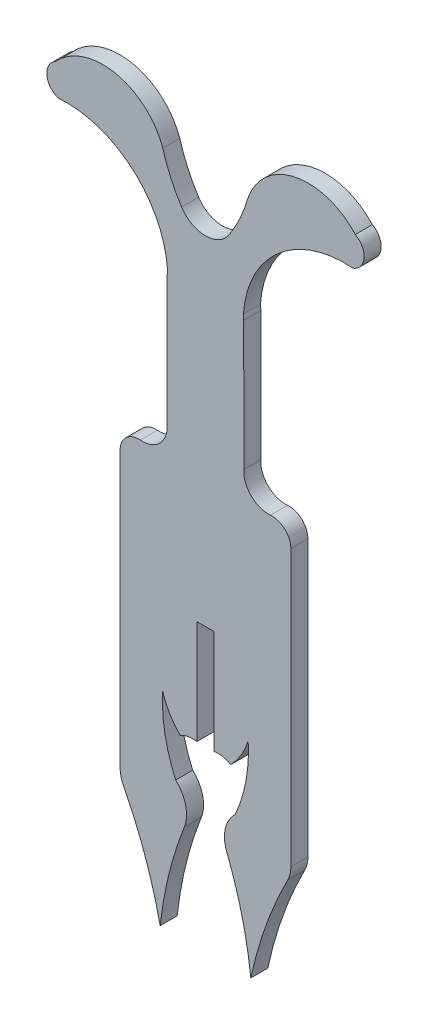
SolidWorks part; units mm, degrees
ref_plane "Front Plane" through (0, 0, 0) normal (0, 0, 1) x (1, 0, 0)
ref_plane "Top Plane" through (0, 0, 0) normal (0, 1, 0) x (1, 0, 0)
ref_plane "Right Plane" through (0, 0, 0) normal (1, 0, 0) x (0, 0, -1)
sketch "Sketch1" plane through (0, 0, 0) normal (0, 0, 1) x (1, 0, 0)
  line L0 (0.7584, -14.5146) -> (0.7564, -5.2296)
  line L1 (0.7564, -5.2296) -> (-0.7676, -5.2286)
  line L2 (-0.7676, -5.2286) -> (-0.7676, -14.5136)
  line L3 (-7.6306, -20.0152) -> (-7.6319, 4.6269)
  line L4 (-3.4282, 8.6563) -> (-3.4315, 20.1838)
  line L5 (3.42, 20.1837) -> (3.4215, 8.6564)
  line L6 (7.6282, 4.629) -> (7.6318, -20.0085)
  line L7 (-0.001, -5.2309) -> (-0.001, 45.1818) construction
  arc A0 (-0.7676, -14.5136) -> (-2.2638, -14.7873) centre (-1.1294, -16.7622) ccw
  arc A1 (-1.9033, -21.7277) -> (-2.6639, -18.445) centre (-4.6657, -20.6383) ccw
  arc A2 (-5.8206, 6.2988) -> (-7.6319, 4.6269) centre (-5.9547, 4.627) ccw
  arc A3 (-5.8206, 6.2988) -> (-3.4282, 8.6563) centre (-5.643, 8.5113) ccw
  arc A4 (3.42, 20.1837) -> (3.3881, 20.6504) centre (-0.0057, 20.1837) ccw
  arc A5 (3.4215, 8.6564) -> (5.8136, 6.3009) centre (5.6367, 8.5136) ccw
  arc A6 (7.6282, 4.629) -> (5.8136, 6.3009) centre (5.9508, 4.629) ccw
  arc A7 (2.6574, -18.4469) -> (1.9018, -21.7289) centre (4.6686, -20.6379) ccw
  arc A8 (2.2578, -14.7885) -> (0.7584, -14.5146) centre (1.1225, -16.7628) ccw
  arc A9 (-7.3492, -21.1771) -> (-4.0522, -30.4103) centre (-40.4269, -38.1939) cw
  arc A10 (-4.0522, -30.4103) -> (-1.9033, -21.7277) centre (29.4651, -34.0981) cw
  arc A11 (-2.6639, -18.445) -> (-3.8253, -12.1547) centre (9.6354, -12.9218) cw
  arc A12 (-3.8253, -12.1547) -> (-2.2638, -14.7873) centre (2.2306, -10.3421) ccw
  arc A13 (3.8188, -12.1565) -> (2.2578, -14.7885) centre (-2.2372, -10.3439) cw
  arc A14 (2.6574, -18.4469) -> (3.8188, -12.1565) centre (-9.6419, -12.9236) ccw
  arc A15 (4.0502, -30.4103) -> (1.9018, -21.7289) centre (-29.4671, -34.0983) ccw
  arc A16 (7.3502, -21.1712) -> (4.0502, -30.4103) centre (40.4249, -38.1939) ccw
  arc A17 (7.6318, -20.0085) -> (7.3502, -21.1712) centre (5.0918, -20.0088) cw
  arc A18 (-7.3492, -21.1771) -> (-7.6306, -20.0152) centre (-5.0906, -20.0151) cw
  arc A19 (3.3881, 20.6504) -> (13.1804, 29.1097) centre (12.4641, 20.0416) cw
  arc A20 (13.1804, 29.1097) -> (13.3948, 31.8231) centre (12.7, 30.5128) ccw
  arc A21 (13.3948, 31.8231) -> (3.8188, 29.9087) centre (9.1771, 28.0133) ccw
  arc A22 (3.8188, 29.9087) -> (2.1342, 26.1867) centre (-9.5644, 33.7235) cw
  arc A23 (2.1342, 26.1867) -> (-2.1362, 26.1867) centre (-0.001, 27.5623) cw
  arc A24 (-3.8208, 29.9087) -> (-2.1362, 26.1867) centre (9.5624, 33.7235) ccw
  arc A25 (-13.3968, 31.8231) -> (-3.8208, 29.9087) centre (-9.1791, 28.0133) cw
  arc A26 (-13.1824, 29.1097) -> (-13.3968, 31.8231) centre (-12.702, 30.5128) cw
  arc A27 (-3.3901, 20.6504) -> (-13.1824, 29.1097) centre (-12.4661, 20.0416) ccw
  arc A28 (-3.4315, 20.1838) -> (-3.3901, 20.6504) centre (-0.0064, 20.1152) cw
extrude "Boss-Extrude1" add sketch "Sketch1" along normal blind 1.524
